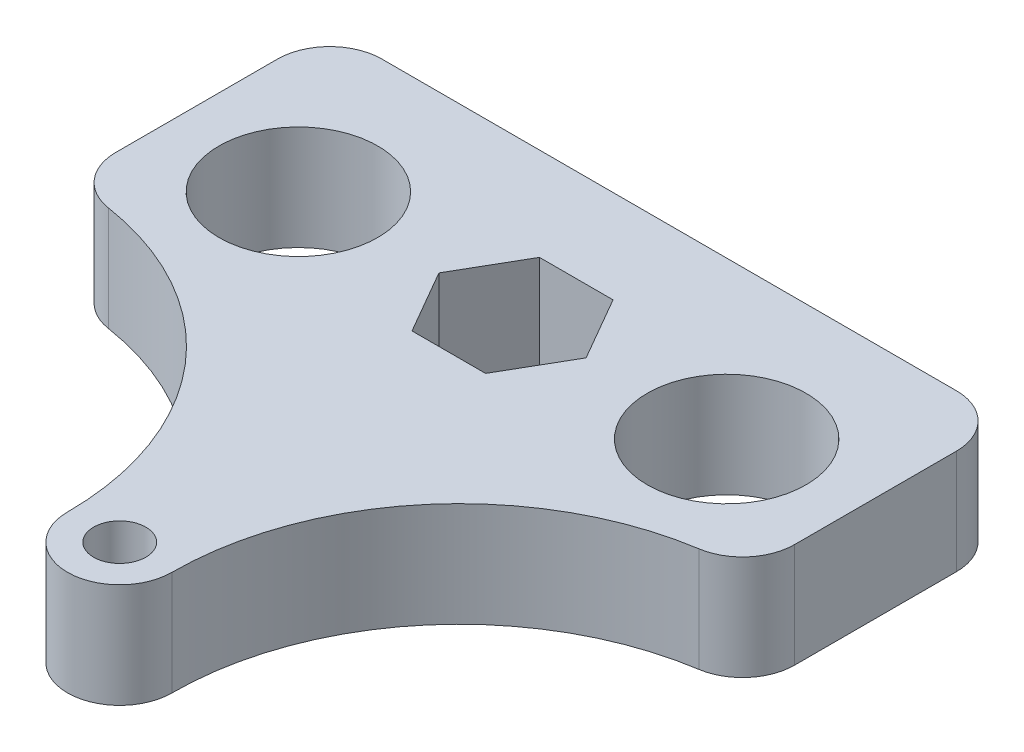
SolidWorks part; units mm, degrees
ref_plane "Alzado" through (0, 0, 0) normal (0, 0, 1) x (1, 0, 0)
ref_plane "Planta" through (0, 0, 0) normal (0, 1, 0) x (1, 0, 0)
ref_plane "Vista lateral" through (0, 0, 0) normal (1, 0, 0) x (0, 0, -1)
sketch "Sketch1" plane through (0, 0, 0) normal (0, 1, 0) x (1, 0, 0)
  line L0 (-27.5, 25.1) -> (27.5, 25.1)
  line L1 (32.5, 20.1) -> (32.5, 4.6131)
  line L6 (7.0437, 10.1) -> (3.5218, 16.2)
  line L7 (3.5218, 16.2) -> (-3.5218, 16.2)
  line L8 (-3.5218, 16.2) -> (-7.0437, 10.1)
  line L9 (-7.0437, 10.1) -> (-3.5218, 4)
  line L10 (-3.5218, 4) -> (3.5218, 4)
  line L11 (3.5218, 4) -> (7.0437, 10.1)
  line L13 (-5, -27.5) -> (5, -27.5) construction
  line L16 (-32.5, 4.6131) -> (-32.5, 20.1)
  circle A2 centre (0, 10.1) radius 6.1 construction
  circle A3 centre (-20.5, 10.1) radius 7.6
  circle A4 centre (20.5, 10.1) radius 7.6
  arc A6 (-5, -27.5) -> (5, -27.5) centre (0, -27.5) ccw
  circle A7 centre (0, -27.5) radius 2.5
  arc A8 (5, -27.5) -> (28.2692, -0.3274) centre (32.5, -27.5) cw
  arc A9 (-5, -27.5) -> (-28.2692, -0.3274) centre (-32.5, -27.5) ccw
  arc A10 (27.5, 25.1) -> (32.5, 20.1) centre (27.5, 20.1) cw
  arc A11 (-27.5, 25.1) -> (-32.5, 20.1) centre (-27.5, 20.1) ccw
  arc A12 (-28.2692, -0.3274) -> (-32.5, 4.6131) centre (-27.5, 4.6131) cw
  arc A13 (28.2692, -0.3274) -> (32.5, 4.6131) centre (27.5, 4.6131) ccw
  point P4 (0, 0)
  point P5 (0, 25.1)
  point P10 (0, 0)
  point P25 (0, 0)
  point P29 (0, 0)
  point P30 (20.5, 10.1)
  point P33 (32.5, 25.1)
  point P36 (-32.5, 25.1)
  point P39 (-32.5, 0)
  point P42 (32.5, 0)
  dimension "D2" = 5
  dimension "D4" = 15.2
  dimension "D8" = 5
  dimension "D9" = 12
  dimension "D7" = 27.5
  dimension "D11" = 5
  dimension "D1" = 65
  dimension "D3" = 12.2
  dimension "D5" = 15
  dimension "D6" = 12
  dimension "D10" = 37.6
extrude "Boss-Extrude1" add sketch "Sketch1" along normal blind 10
